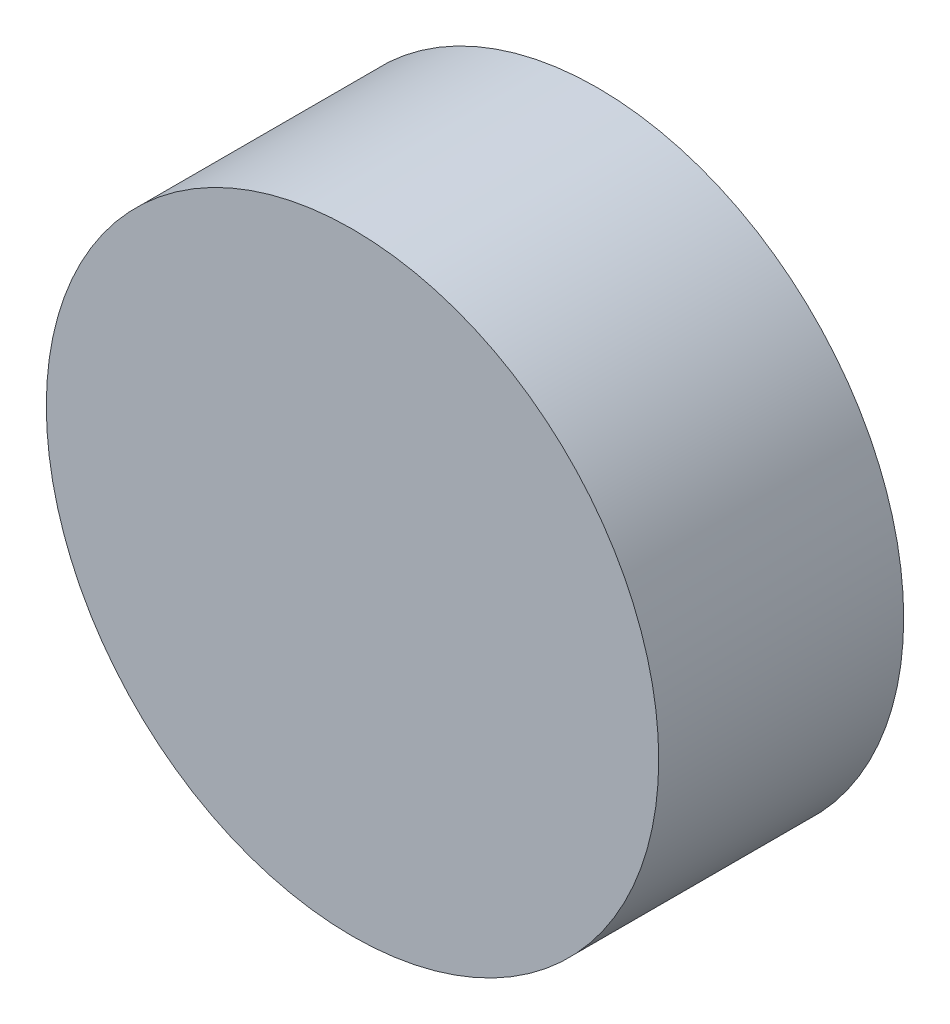
SolidWorks part; units mm, degrees
ref_plane "Ebene vorne" through (0, 0, 0) normal (0, 0, 1) x (1, 0, 0)
ref_plane "Ebene oben" through (0, 0, 0) normal (0, 1, 0) x (1, 0, 0)
ref_plane "Ebene rechts" through (0, 0, 0) normal (1, 0, 0) x (0, 0, -1)
sketch "Skizze1" plane through (0, 0, 0) normal (0, 0, 1) x (1, 0, 0)
  circle A0 centre (0, 0) radius 2.5
  dimension "D1" = 5
extrude "Aufsatz-Linear austragen1" add sketch "Skizze1" along normal blind 2
